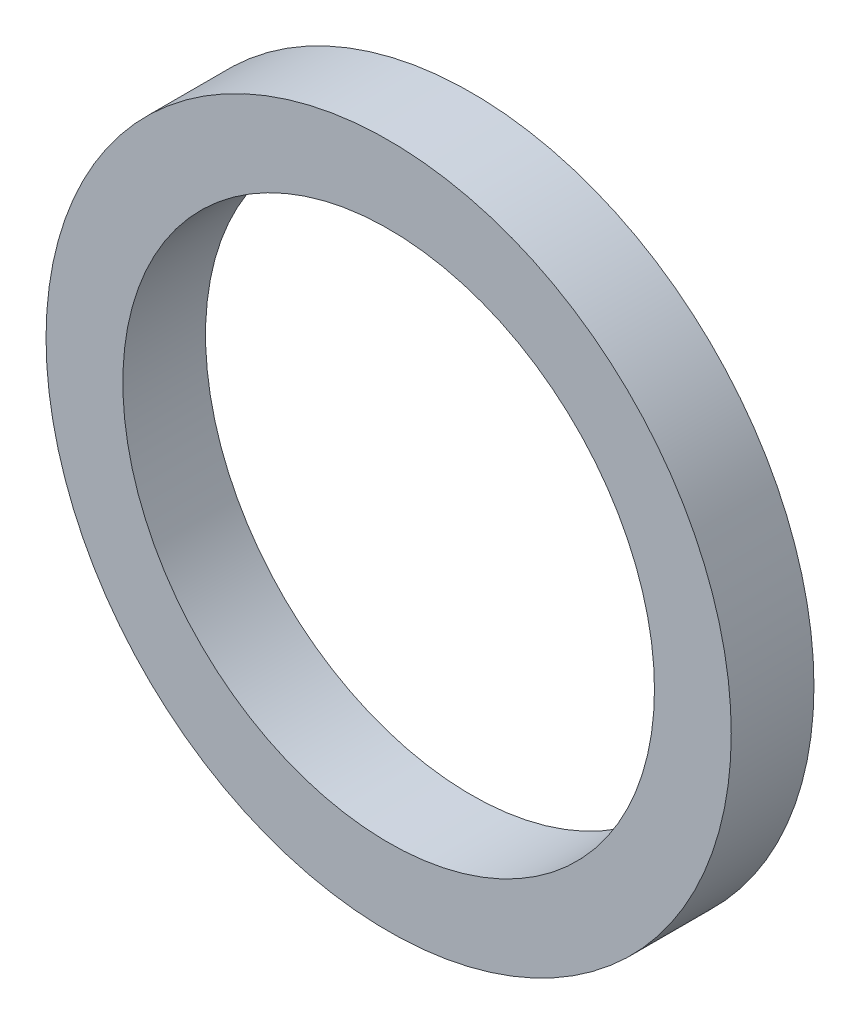
SolidWorks part; units mm, degrees
material "1023 Carbon Steel Sheet (SS)"
ref_plane "Front Plane" through (0, 0, 0) normal (0, 0, 1) x (1, 0, 0)
ref_plane "Top Plane" through (0, 0, 0) normal (0, 1, 0) x (1, 0, 0)
ref_plane "Right Plane" through (0, 0, 0) normal (1, 0, 0) x (0, 0, -1)
sketch "Sketch1" plane through (0, 0, 0) normal (0, 0, 1) x (1, 0, 0)
  circle A0 centre (0, 0) radius 22.5
  circle A1 centre (0, 0) radius 29
  dimension "D1" = 45
  dimension "D2" = 58
extrude "Boss-Extrude1" add sketch "Sketch1" along normal mid plane 7
